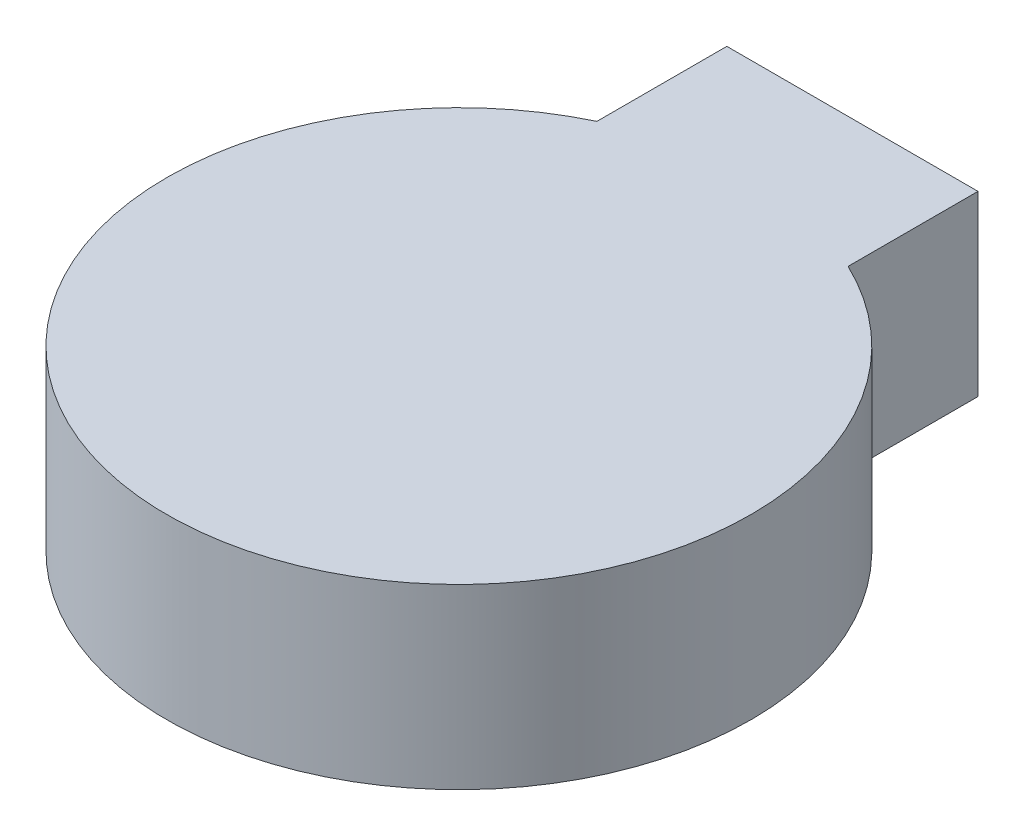
SolidWorks part; units mm, degrees
ref_plane "Front Plane" through (0, 0, 0) normal (0, 0, 1) x (1, 0, 0)
ref_plane "Top Plane" through (0, 0, 0) normal (0, 1, 0) x (1, 0, 0)
ref_plane "Right Plane" through (0, 0, 0) normal (1, 0, 0) x (0, 0, -1)
sketch "Sketch1" plane through (0, 0, 0) normal (0, 1, 0) x (1, 0, 0)
  line L0 (-4.9459, 15.5) -> (4.9459, 15.5)
  line L2 (4.9459, 15.5) -> (4.9459, 10.3821)
  line L3 (4.9459, 10.3821) -> (-4.9459, 10.3821) construction
  line L4 (-4.9459, 10.3821) -> (-4.9459, 15.5)
  arc A0 (-4.9459, 10.3821) -> (4.9459, 10.3821) centre (0, 0) ccw
  dimension "D1" = 23
  dimension "D2" = 5.1179
  dimension "D3" = 9.8918
extrude "Boss-Extrude1" add sketch "Sketch1" along normal blind 7
